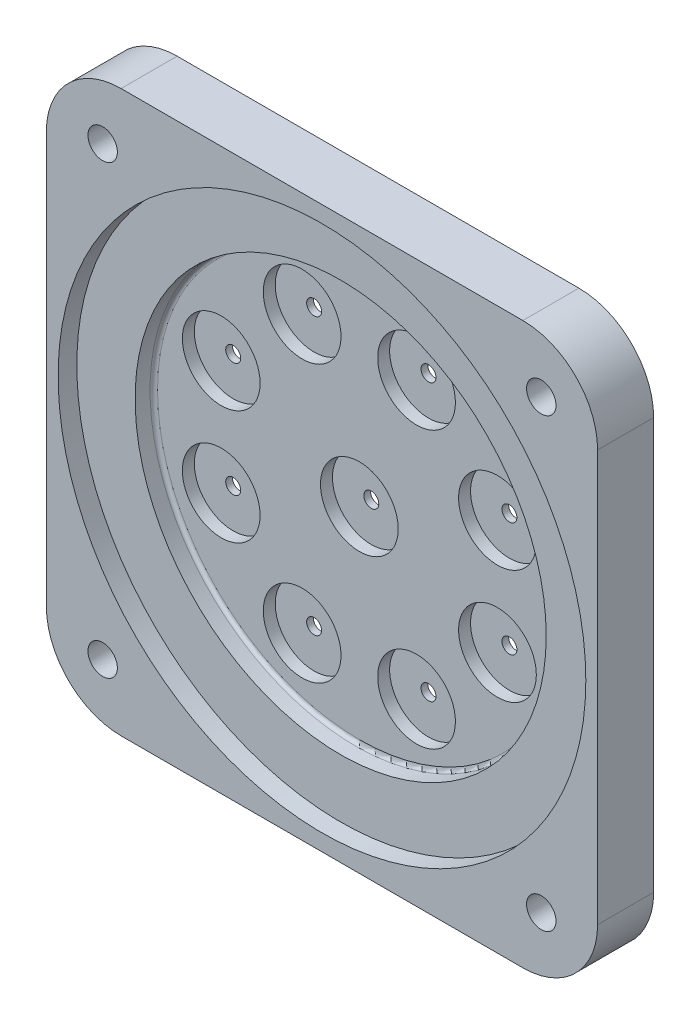
SolidWorks part; units mm, degrees
material "ABS"
ref_plane "Front Plane" through (0, 0, 0) normal (0, 0, 1) x (1, 0, 0)
ref_plane "Top Plane" through (0, 0, 0) normal (0, 1, 0) x (1, 0, 0)
ref_plane "Right Plane" through (0, 0, 0) normal (1, 0, 0) x (0, 0, -1)
sketch "Sketch1" plane through (0, 0, 0) normal (0, 0, 1) x (1, 0, 0)
  line L0 (-93.6625, 0) -> (93.6625, 0) construction
  line L1 (0, 95.25) -> (0, -95.25) construction
  line L8 (93.6625, 69.85) -> (93.6625, -69.85)
  line L9 (68.2625, -95.25) -> (-68.2625, -95.25)
  line L10 (-93.6625, -69.85) -> (-93.6625, 69.85)
  line L11 (-68.2625, 95.25) -> (68.2625, 95.25)
  circle A1 centre (0, 0) radius 89.662 construction
  arc A3 (-68.2625, -95.25) -> (-93.6625, -69.85) centre (-68.2625, -69.85) cw
  arc A4 (93.6625, -69.85) -> (68.2625, -95.25) centre (68.2625, -69.85) cw
  arc A5 (93.6625, 69.85) -> (68.2625, 95.25) centre (68.2625, 69.85) ccw
  arc A6 (-93.6625, 69.85) -> (-68.2625, 95.25) centre (-68.2625, 69.85) cw
  point P6 (0, 0)
  point P15 (0, 0)
  dimension "D4" = 179.324
  dimension "D5" = 25.4
  dimension "D3" = 190.5
extrude "Boss-Extrude1" add sketch "Sketch1" along normal blind 19.05
sketch "Sketch4" plane through (0, 0, 0) normal (0, 0, 1) x (1, 0, 0)
  circle A0 centre (0, 0) radius 89.662
  dimension "D2" = 179.324
extrude "Inset Rim" cut sketch "Sketch4" against normal blind 6.35 from offset 19.05
sketch "Sketch9" plane through (0, 0, 0) normal (0, 0, 1) x (1, 0, 0)
  circle A0 centre (0, 0) radius 69.85
  dimension "D1" = 139.7
extrude "Cut-Extrude1" cut sketch "Sketch9" against normal blind 6.35 from surface at 12.7 starting at face at (89.662, 0, 12.7)
fillet "Fillet2" radius 1.27 1 edges at (69.85, 0, 6.35)
sketch "Sketch10" plane through (0, 0, 0) normal (0, 0, -1) x (-1, 0, 0)
  line L0 (-86.223, 87.8105) -> (-62.8197, 63.9763) construction
  line L1 (86.223, 87.8105) -> (62.8197, 63.9763) construction
  line L2 (86.223, -87.8105) -> (62.8197, -63.9763) construction
  arc A0 (-68.2625, 95.25) -> (-93.6625, 69.85) centre (-68.2625, 69.85) ccw construction
  circle A1 centre (0, 0) radius 89.662 construction
  arc A2 (93.6625, 69.85) -> (68.2625, 95.25) centre (68.2625, 69.85) ccw construction
  arc A3 (68.2625, -95.25) -> (93.6625, -69.85) centre (68.2625, -69.85) ccw construction
  point P10 (-74.5213, 75.8934)
  point P20 (74.5213, 75.8934)
  point P30 (74.5213, -75.8934)
  point P32 (-74.5213, -75.8934)
hole_wizard "CBORE for M8 Hex Head Bolt1" positions "Sketch10" profile "Sketch11" counterbore size "M8" standard "ISO" end condition through all
sketch "Sketch11" plane through (74.5213, -75.8934, 0) normal (1, 0, 0) x (0, 1, 0)
  line L0 (0, 0) -> (0, 19.05)
  line L1 (0, 19.05) -> (5, 19.05)
  line L3 (5, 19.05) -> (5, 5.3)
  line L4 (5, 5.3) -> (9.0055, 5.3)
  line L5 (9.0055, 5.3) -> (9.0055, 0)
  line L7 (9.0055, 0) -> (0, 0)
  line L11 (0, -6.35) -> (0, 107.95) construction
  dimension "Thru Hole Dia." = 10
  dimension "Thru Hole Depth" = 19.05
  dimension "C'Bore Dia." = 18.011
  dimension "C'Bore Depth" = 5.3
sketch "Sketch12" plane through (0, 0, 0) normal (0, 0, -1) x (-1, 0, 0)
  line L0 (19.4403, 46.9331) -> (0, 0) construction
  line L1 (11.7318, 0) -> (5.8659, 10.16) construction
  line L2 (5.8659, 10.16) -> (-5.8659, 10.16) construction
  line L3 (-5.8659, 10.16) -> (-11.7318, 0) construction
  line L4 (-11.7318, 0) -> (-5.8659, -10.16) construction
  line L5 (-5.8659, -10.16) -> (5.8659, -10.16) construction
  line L6 (5.8659, -10.16) -> (11.7318, 0) construction
  line L13 (0, 0) -> (0, 10.16) construction
  line L14 (2.54, 0) -> (0, 0) construction
  line L15 (0, 0) -> (0, 50.8) construction
  circle A0 centre (0, 0) radius 2.54
  circle A1 centre (0, 0) radius 10.16 construction
  circle A3 centre (19.4403, 46.9331) radius 2.54
  circle A13 centre (0, 0) radius 50.8 construction
  circle A14 centre (46.9331, 19.4403) radius 2.54
  circle A15 centre (46.9331, -19.4403) radius 2.54
  circle A16 centre (19.4403, -46.9331) radius 2.54
  circle A17 centre (-19.4403, -46.9331) radius 2.54
  circle A18 centre (-46.9331, -19.4403) radius 2.54
  circle A19 centre (-46.9331, 19.4403) radius 2.54
  circle A20 centre (-19.4403, 46.9331) radius 2.54
  point P33 (0, 0)
  point P38 (0, 0)
  dimension "D1" = 5.08
  dimension "D2" = 20.32
  dimension "D4" = 22.5
  dimension "D3" = 50.8
  dimension "D5" = 8
extrude "Cut-Extrude2" cut sketch "Sketch12" against normal up to surface (6.35 mm away) up to face at (68.58, 0, 6.35)
sketch "Sketch13" plane through (0, 0, 6.35) normal (0, 0, 1) x (1, 0, 0)
  circle A0 centre (0, 0) radius 50.8 construction
  circle A9 centre (46.9331, 19.4403) radius 13.208
  circle A10 centre (19.4403, 46.9331) radius 13.208
  circle A11 centre (19.4403, 46.9331) radius 13.208
  circle A12 centre (46.9331, -19.4403) radius 13.208
  circle A13 centre (19.4403, -46.9331) radius 13.208
  circle A14 centre (0, 0) radius 13.208
  circle A15 centre (0, 0) radius 13.208
  circle A16 centre (-19.4403, -46.9331) radius 13.208
  circle A17 centre (-46.9331, -19.4403) radius 13.208
  circle A19 centre (-46.9331, 19.4403) radius 13.208
  circle A20 centre (-19.4403, 46.9331) radius 13.208
  point P20 (0, 0)
  point P21 (0, 0)
  dimension "D1" = 10.668
  dimension "D2" = 10.668
  dimension "D3" = 8
extrude "Cut-Extrude3" cut sketch "Sketch13" against normal blind 4.064
